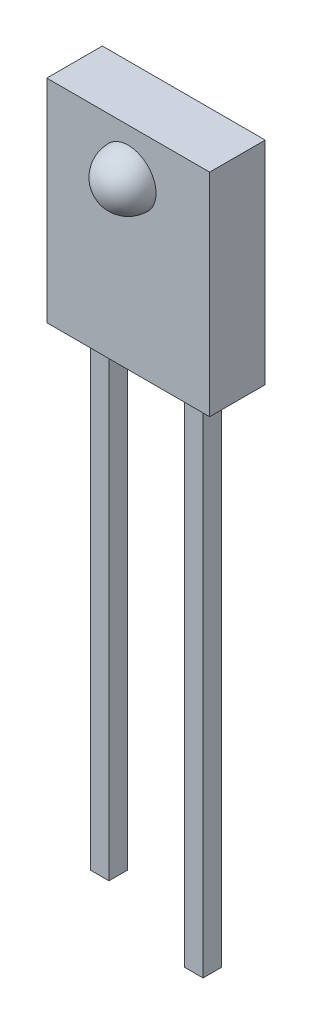
SolidWorks part; units mm, degrees
ref_plane "Front Plane" through (0, 0, 0) normal (0, 0, 1) x (1, 0, 0)
ref_plane "Top Plane" through (0, 0, 0) normal (0, 1, 0) x (1, 0, 0)
ref_plane "Right Plane" through (0, 0, 0) normal (1, 0, 0) x (0, 0, -1)
sketch "Sketch1" plane through (0, 0, 0) normal (0, 0, 1) x (1, 0, 0)
  line L1 (-2.1971, 2.8575) -> (2.1971, 2.8575)
  line L2 (-2.1971, 2.8575) -> (-2.1971, -2.8575)
  line L3 (-2.1971, -2.8575) -> (2.1971, -2.8575)
  line L4 (2.1971, 2.8575) -> (2.1971, -2.8575)
  line L5 (-2.1971, 2.8575) -> (2.1971, -2.8575) construction
  line L6 (-2.1971, -2.8575) -> (2.1971, 2.8575) construction
  point P0 (0, 0)
  dimension "D1" = 4.3942
  dimension "D2" = 5.715
extrude "Boss-Extrude1" add sketch "Sketch1" against normal mid plane 1.4986
sketch "Sketch3" plane through (0, 0, 0) normal (1, 0, 0) x (0, 0, -1)
  line L0 (-2.079, 1.6375) -> (1.7354, 1.6375) construction
  line L1 (-0.7493, -2.8575) -> (-0.7493, 2.8575) construction
  line L2 (-1.4993, 1.6375) -> (-0.7493, 1.6375)
  line L3 (-0.7493, 1.6375) -> (-0.7493, 2.3875)
  line L4 (0.7493, 2.8575) -> (-0.7493, 2.8575) construction
  arc A0 (-0.7493, 2.3875) -> (-1.4993, 1.6375) centre (-0.7493, 1.6375) ccw
  dimension "D1" = 1.22
  dimension "D2" = 0.75
revolve "Revolve1" add sketch "Sketch3" angle 360 about L0
sketch "Sketch4" plane through (0, 0, 0) normal (0, 0, 1) x (1, 0, 0)
  line L0 (-1.27, -2.8575) -> (1.27, -2.8575) construction
  line L1 (-2.1971, -2.8575) -> (2.1971, -2.8575) construction
  line L3 (-1.52, -2.8575) -> (-1.02, -2.8575)
  line L4 (-1.52, -2.8575) -> (-1.52, -15.5575)
  line L5 (-1.52, -15.5575) -> (-1.02, -15.5575)
  line L6 (-1.02, -2.8575) -> (-1.02, -15.5575)
  line L7 (1.02, -2.8575) -> (1.52, -2.8575)
  line L8 (1.02, -2.8575) -> (1.02, -16.5575)
  line L9 (1.02, -16.5575) -> (1.52, -16.5575)
  line L10 (1.52, -2.8575) -> (1.52, -16.5575)
  point P4 (0, -2.8575)
  point P14 (1.27, -16.5575)
  point P15 (-1.27, -15.5575)
  dimension "D1" = 2.54
  dimension "D2" = 0.5
  dimension "D3" = 12.7
  dimension "D4" = 1
extrude "Boss-Extrude2" add sketch "Sketch4" along normal mid plane 0.5
